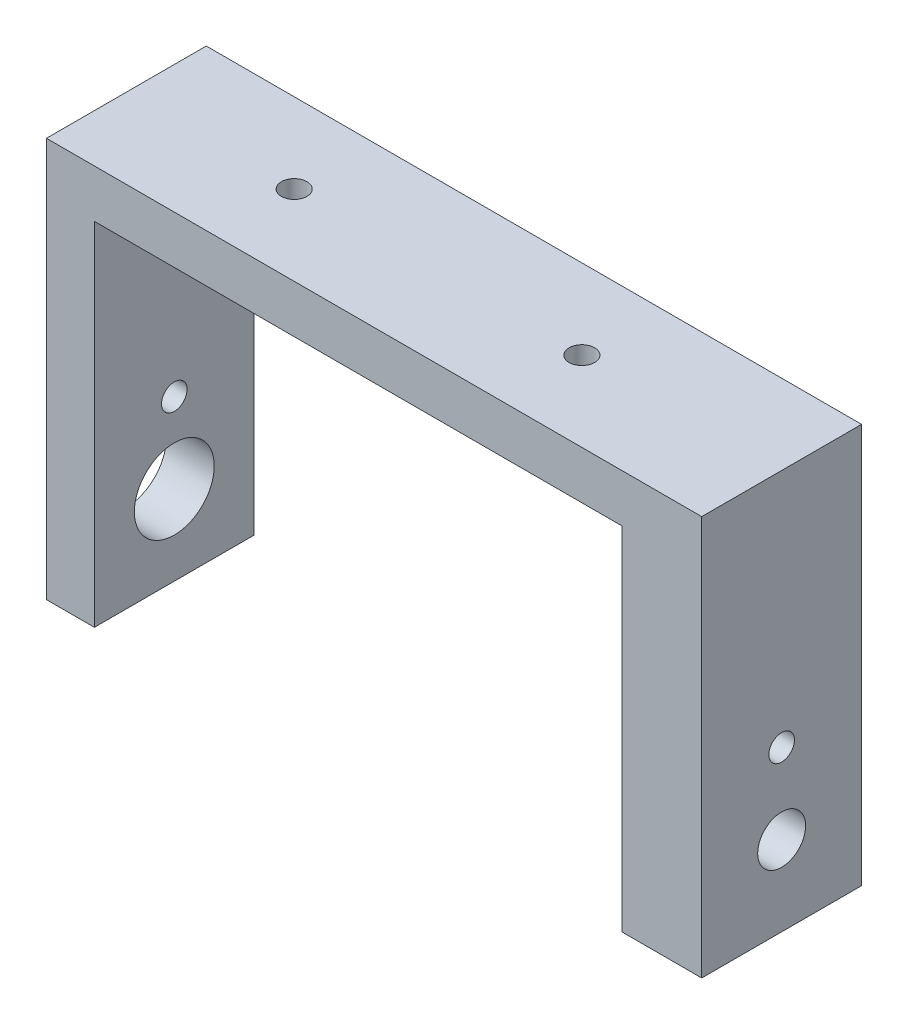
SolidWorks part; units mm, degrees
ref_plane "Front Plane" through (0, 0, 0) normal (0, 0, 1) x (1, 0, 0)
ref_plane "Top Plane" through (0, 0, 0) normal (0, 1, 0) x (1, 0, 0)
ref_plane "Right Plane" through (0, 0, 0) normal (1, 0, 0) x (0, 0, -1)
sketch "Sketch1" plane through (0, 0, 0) normal (0, 0, 1) x (1, 0, 0)
  line L1 (-16.5, 11) -> (16.5, 11)
  line L2 (-16.5, 11) -> (-16.5, -11)
  line L3 (-16.5, -11) -> (16.5, -11)
  line L4 (16.5, 11) -> (16.5, -11)
  line L5 (-16.5, 11) -> (16.5, -11) construction
  line L6 (-16.5, -11) -> (16.5, 11) construction
  line L7 (-19.5, -14) -> (19.5, -14)
  line L8 (-19.5, -14) -> (-19.5, 14)
  line L9 (-19.5, 14) -> (19.5, 14)
  line L10 (19.5, -14) -> (19.5, 14)
  line L11 (-19.5, -14) -> (19.5, 14) construction
  line L12 (-19.5, 14) -> (19.5, -14) construction
  line L13 (-19.5, -14) -> (21.5, -14)
  line L14 (-19.5, -14) -> (-19.5, 14)
  line L15 (-19.5, 14) -> (21.5, 14)
  line L16 (21.5, -14) -> (21.5, 14)
  point P0 (0, 0)
  point P6 (0, 0)
  dimension "D1" = 33
  dimension "D2" = 3
  dimension "D3" = 3
  dimension "D4" = 22
  dimension "D5" = 5
sketch "Sketch2" plane through (0, 0, 0) normal (0, 0, 1) x (1, 0, 0)
  line L0 (-16.5, -11) -> (-19.5, -11)
  line L1 (-19.5, -14) -> (-19.5, 14) construction
  line L2 (-19.5, -11) -> (-19.5, 14)
  line L3 (21.5, 14) -> (-19.5, 14)
  line L4 (16.5, -11) -> (21.5, -11)
  line L6 (21.5, -14) -> (21.5, 14) construction
  line L7 (16.5, -11) -> (16.5, 11)
  line L8 (16.5, 11) -> (-16.5, 11)
  line L9 (-16.5, 11) -> (-16.5, -11)
  line L10 (21.5, -11) -> (21.5, 14)
extrude "Boss-Extrude1" add sketch "Sketch2" along normal blind 10
sketch "Sketch3" plane through (-19.5, 0, 0) normal (-1, 0, 0) x (0, 0, 1)
  line L0 (5, 14) -> (5, -11) construction
  line L1 (10, 14) -> (0, 14) construction
  line L2 (10, -11) -> (0, -11) construction
  line L3 (0, -6) -> (10, -6)
  line L4 (10, 14) -> (10, -11) construction
  line L5 (0, -1) -> (10, -1)
  point P11 (5, -6)
  point P14 (5, -1)
  dimension "D1" = 5
  dimension "D2" = 5
sketch "Sketch4" plane through (-19.5, 0, 0) normal (-1, 0, 0) x (0, 0, 1)
  circle A0 centre (5, -6) radius 1.5
  circle A1 centre (5, -1) radius 0.8
extrude "Cut-Extrude1" cut sketch "Sketch4" against normal through all
sketch "Sketch5" plane through (0, 14, 0) normal (0, 1, 0) x (1, 0, 0)
  line L0 (-19.5, -5) -> (21.5, -5) construction
  line L1 (-19.5, -10) -> (-19.5, 0) construction
  line L2 (21.5, -10) -> (21.5, 0) construction
  line L3 (-9, 0) -> (-9, -10)
  line L4 (21.5, -10) -> (-19.5, -10) construction
  line L5 (9, 0) -> (9, -10)
  point P6 (1, -5)
  point P11 (-9, -5)
  point P14 (9, -5)
  point P15 (0, -5)
  dimension "D1" = 9
  dimension "D2" = 9
  dimension "D3" = 1
sketch "Sketch6" plane through (0, 14, 0) normal (0, 1, 0) x (1, 0, 0)
  line L0 (9, 0) -> (9, -10) construction
  circle A0 centre (-9, -5) radius 0.8
  circle A1 centre (9, -5) radius 0.8
extrude "Cut-Extrude2" cut sketch "Sketch6" against normal through all
sketch "Sketch7" plane through (16.5, 0, 0) normal (-1, 0, 0) x (0, 0, 1)
  line L0 (0, -11) -> (0, 12)
  line L1 (0, 11) -> (0, -11) construction
  line L2 (10, -11) -> (0, -11) construction
  line L3 (0, 12) -> (10, 12)
  line L4 (10, 11) -> (10, -11) construction
  point P5 (1, -11)
  point P6 (9, -11)
  point P13 (3, 12)
  point P14 (7, 12)
  point P15 (1, -1)
  point P16 (9, -1)
  dimension "D1" = 1
  dimension "D2" = 1
  dimension "D3" = 3
  dimension "D4" = 3
  dimension "D5" = 10
  dimension "D6" = 1
  dimension "D7" = 10
  dimension "D8" = 1
  dimension "D9" = 13
sketch "Sketch8" plane through (16.5, 0, 0) normal (-1, 0, 0) x (0, 0, 1)
  line L0 (1, -1) -> (1, -11)
  line L1 (3, 12) -> (7, 12)
  line L2 (3, 12) -> (1, -1)
  line L3 (1, -11) -> (9, -11)
  line L5 (7, 12) -> (9, -1)
  line L6 (9, -1) -> (9, -11)
extrude "Cut-Extrude3" cut sketch "Sketch8" against normal blind 2
sketch "Sketch9" plane through (-19.5, 0, 0) normal (-1, 0, 0) x (0, 0, 1)
  circle A0 centre (5, -6) radius 2.5
extrude "Cut-Extrude4" cut sketch "Sketch9" against normal blind 10
